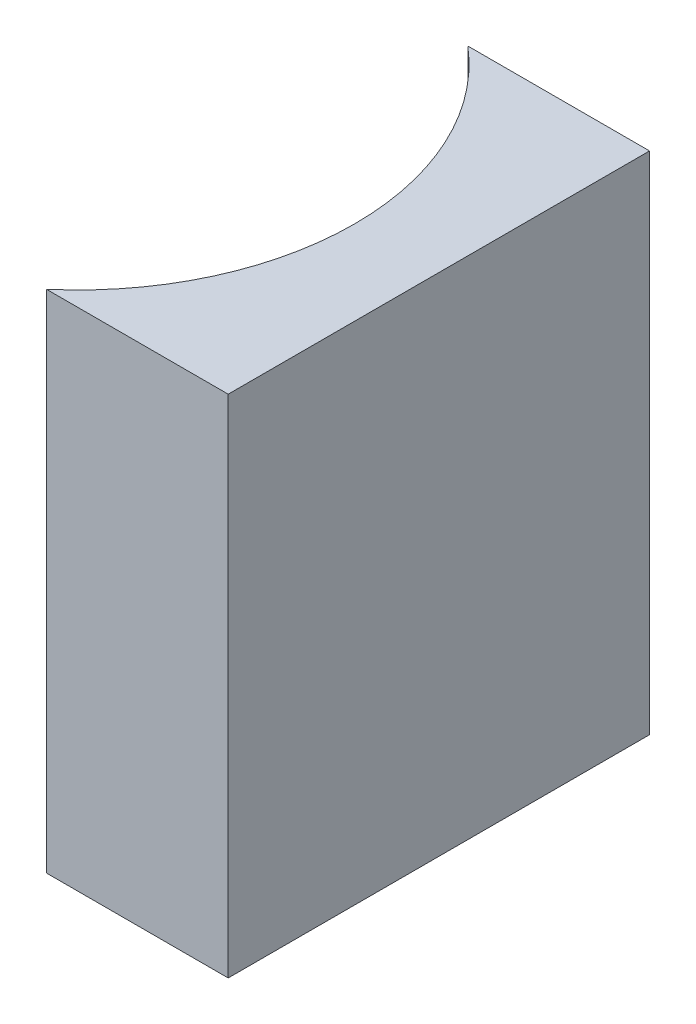
SolidWorks part; units mm, degrees
ref_plane "前视基准面" through (0, 0, 0) normal (0, 0, 1) x (1, 0, 0)
ref_plane "上视基准面" through (0, 0, 0) normal (0, 1, 0) x (1, 0, 0)
ref_plane "右视基准面" through (0, 0, 0) normal (1, 0, 0) x (0, 0, -1)
sketch "草图1" plane through (0, 0, 0) normal (0, 1, 0) x (1, 0, 0)
  line L0 (0, 0) -> (0, -10)
  line L1 (0, 0) -> (-4.3134, 0)
  line L2 (0, -10) -> (-4.3134, -10)
  line L3 (8.2336, -5) -> (-10.4405, -5) construction
  arc A0 (-4.3134, -10) -> (-4.3134, 0) centre (-8.56, -5) ccw
  point P7 (-2, -5)
  point P8 (0, -5)
  dimension "D2" = 6.56
  dimension "D3" = 2
  dimension "D1" = 10
extrude "凸台-拉伸1" add sketch "草图1" along normal blind 12
